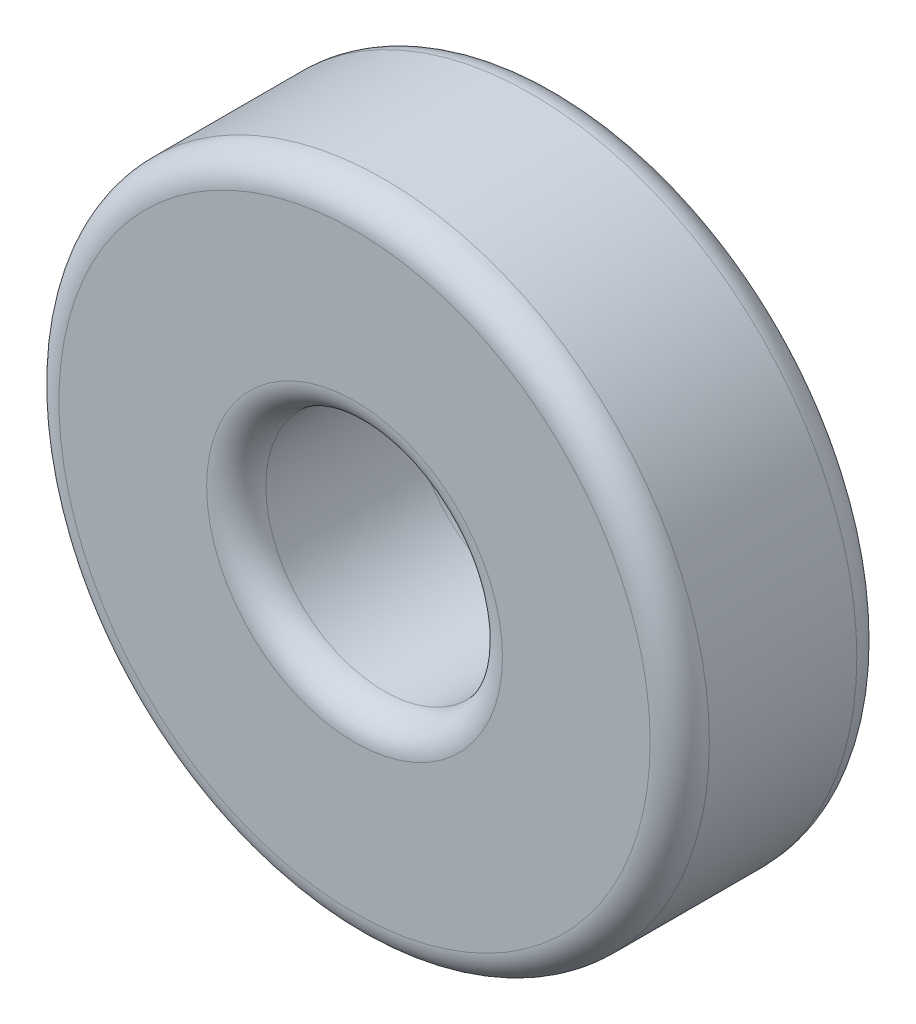
SolidWorks part; units mm, degrees
ref_plane "Front Plane" through (0, 0, 0) normal (0, 0, 1) x (1, 0, 0)
ref_plane "Top Plane" through (0, 0, 0) normal (0, 1, 0) x (1, 0, 0)
ref_plane "Right Plane" through (0, 0, 0) normal (1, 0, 0) x (0, 0, -1)
sketch "Sketch1" plane through (0, 0, 0) normal (0, 0, 1) x (1, 0, 0)
  circle A0 centre (0, 0) radius 10.9919
  circle A1 centre (0, 0) radius 4
  dimension "D1" = 8
  dimension "D2" = 21.9837
extrude "Boss-Extrude1" add sketch "Sketch1" along normal blind 6.985
fillet "Fillet2" radius 1 4 edges at (4, 0, 0) (4, 0, 6.985) (10.9919, 0, 0) (10.9919, 0, 6.985)
